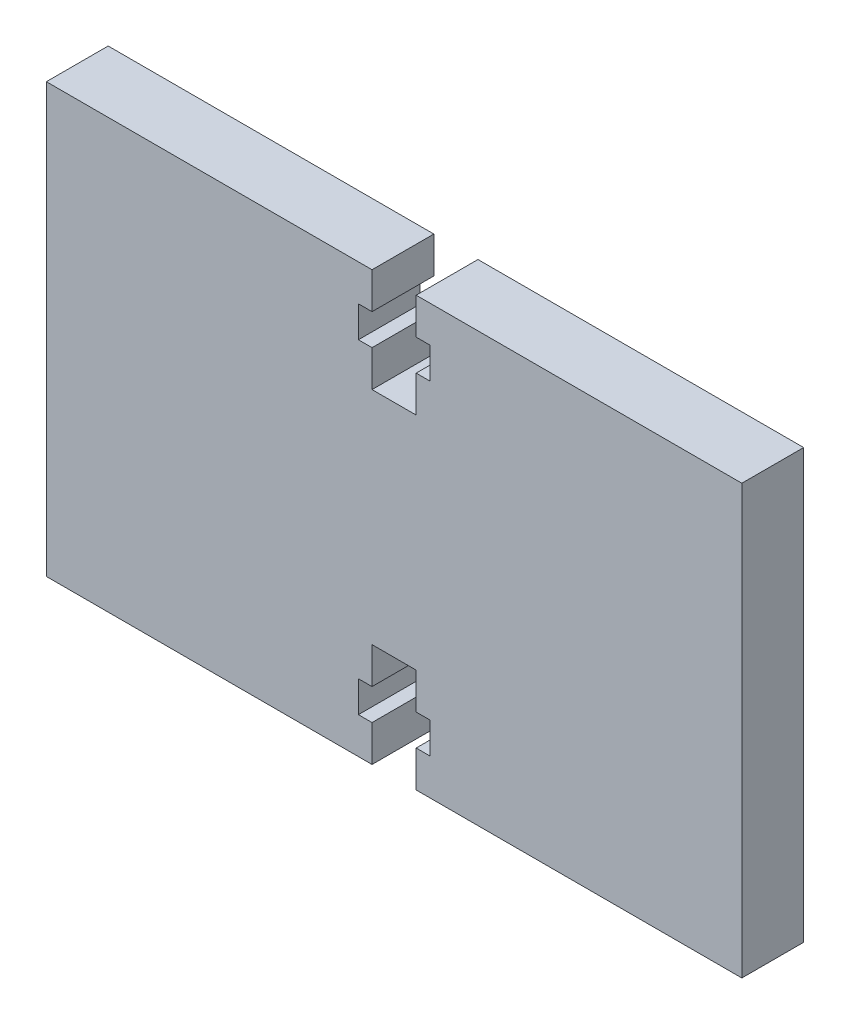
SolidWorks part; units mm, degrees
ref_plane "Front Plane" through (0, 0, 0) normal (0, 0, 1) x (1, 0, 0)
ref_plane "Top Plane" through (0, 0, 0) normal (0, 1, 0) x (1, 0, 0)
ref_plane "Right Plane" through (0, 0, 0) normal (1, 0, 0) x (0, 0, -1)
sketch "Sketch1" plane through (0, 0, 0) normal (0, 0, 1) x (1, 0, 0)
  line L0 (0, 16.51) -> (0, -7.29) construction
  line L1 (1.7, -16.51) -> (1.7, -13.71)
  line L2 (-26.797, -16.51) -> (-26.797, 16.51)
  line L3 (-26.797, 16.51) -> (-1.7, 16.51)
  line L4 (26.797, -16.51) -> (26.797, 16.51)
  line L5 (-26.797, -16.51) -> (26.797, 16.51) construction
  line L6 (-26.797, 16.51) -> (26.797, -16.51) construction
  line L7 (-13.4509, -7.29) -> (13.4509, -7.29) construction
  line L8 (0, 5.91) -> (26.797, 5.91) construction
  line L9 (-1.7, 16.51) -> (-1.7, 13.71)
  line L10 (-1.7, 13.71) -> (-2.75, 13.71)
  line L11 (-2.75, 13.71) -> (-2.75, 11.31)
  line L12 (-2.75, 11.31) -> (-1.7, 11.31)
  line L13 (-1.7, 11.31) -> (-1.7, 8.51)
  line L14 (-1.7, 8.51) -> (1.7, 8.51)
  line L15 (-2.75, 12.51) -> (0, 12.51) construction
  line L16 (1.7, 11.31) -> (1.7, 8.51)
  line L17 (2.75, 11.31) -> (1.7, 11.31)
  line L18 (2.75, 13.71) -> (2.75, 11.31)
  line L19 (1.7, 13.71) -> (2.75, 13.71)
  line L20 (1.7, 16.51) -> (1.7, 13.71)
  line L21 (1.7, 16.51) -> (26.797, 16.51)
  line L22 (0, 0) -> (26.797, 0) construction
  line L23 (1.7, -13.71) -> (2.75, -13.71)
  line L24 (2.75, -13.71) -> (2.75, -11.31)
  line L25 (2.75, -11.31) -> (1.7, -11.31)
  line L26 (1.7, -11.31) -> (1.7, -8.51)
  line L27 (-1.7, -8.51) -> (1.7, -8.51)
  line L28 (-1.7, -11.31) -> (-1.7, -8.51)
  line L29 (-2.75, -11.31) -> (-1.7, -11.31)
  line L30 (-2.75, -13.71) -> (-2.75, -11.31)
  line L31 (-1.7, -13.71) -> (-2.75, -13.71)
  line L32 (-1.7, -16.51) -> (-1.7, -13.71)
  line L33 (1.7, -16.51) -> (26.797, -16.51)
  line L34 (-26.797, -16.51) -> (-1.7, -16.51)
  point P0 (0, 0)
  point P23 (0, 8.51)
  dimension "D1" = 33.02
  dimension "D2" = 53.594
  dimension "D3" = 1.7
  dimension "D4" = 2.75
  dimension "D5" = 8
  dimension "D6" = 4
  dimension "D7" = 2.4
extrude "Boss-Extrude1" add sketch "Sketch1" along normal blind 4.7625
equation "\"D6@Sketch1\"=\"D5@Sketch1\"/2"
